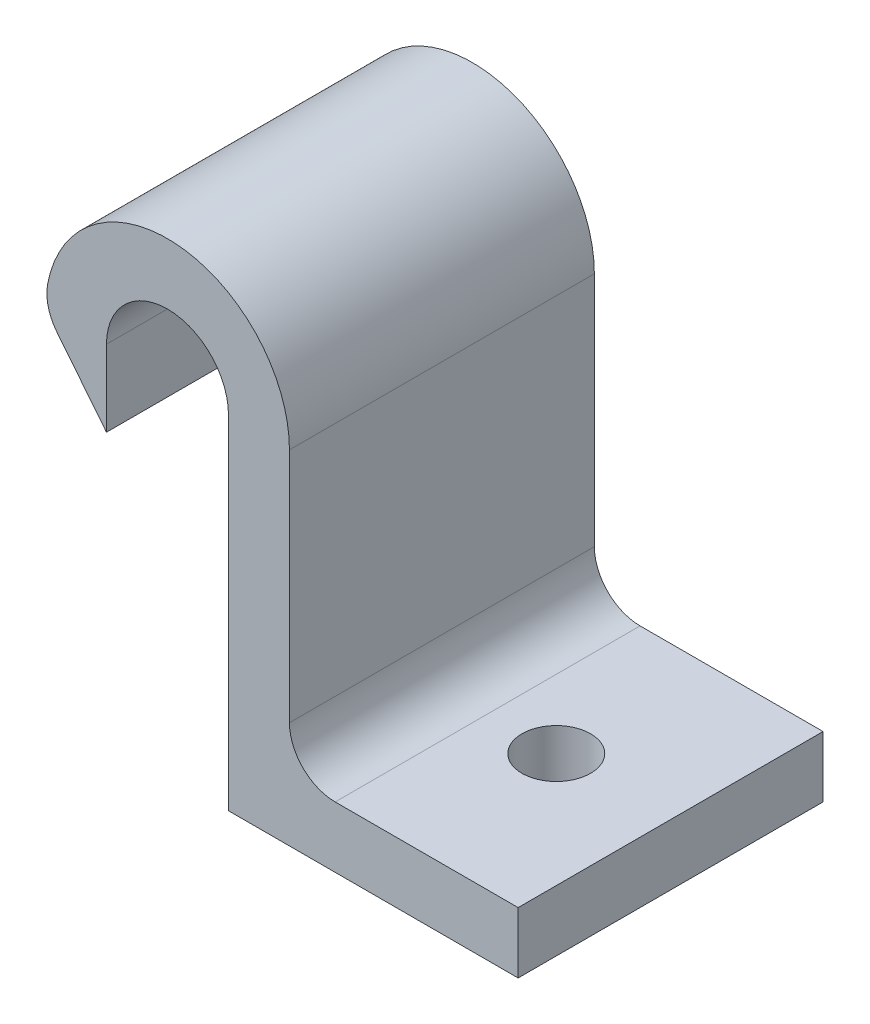
SolidWorks part; units mm, degrees
ref_plane "Alzado" through (0, 0, 0) normal (0, 0, 1) x (1, 0, 0)
ref_plane "Planta" through (0, 0, 0) normal (0, 1, 0) x (1, 0, 0)
ref_plane "Vista lateral" through (0, 0, 0) normal (1, 0, 0) x (0, 0, -1)
sketch "Croquis1" plane through (0, 0, 0) normal (0, 0, 1) x (1, 0, 0)
  line L0 (0, 0) -> (0, 22.5)
  line L1 (0, 0) -> (19, 0)
  line L2 (-8, 22.5) -> (-8, 17.5)
  line L3 (19, 0) -> (19, 4)
  line L4 (19, 4) -> (4, 4)
  line L5 (4, 4) -> (4, 22.5)
  line L6 (-12, 22.5) -> (-8, 17.5)
  arc A0 (0, 22.5) -> (-8, 22.5) centre (-4, 22.5) ccw
  arc A1 (4, 22.5) -> (-12, 22.5) centre (-4, 22.5) ccw
  dimension "D3" = 4
  dimension "D1" = 22.5
  dimension "D2" = 5
  dimension "D4" = 4
  dimension "D5" = 4
  dimension "D6" = 15
extrude "Saliente-Extruir1" add sketch "Croquis1" along normal blind 20
sketch "Croquis2" plane through (0, 4, 0) normal (0, 1, 0) x (1, 0, 0)
  circle A0 centre (11.5, -10) radius 2.25
  dimension "D1" = 4.5
extrude "Cortar-Extruir1" cut sketch "Croquis2" against normal up to vertex (4 mm away)
fillet "Redondeo1" radius 3 2 edges at (-12, 22.5, 10) (4, 4, 10)
